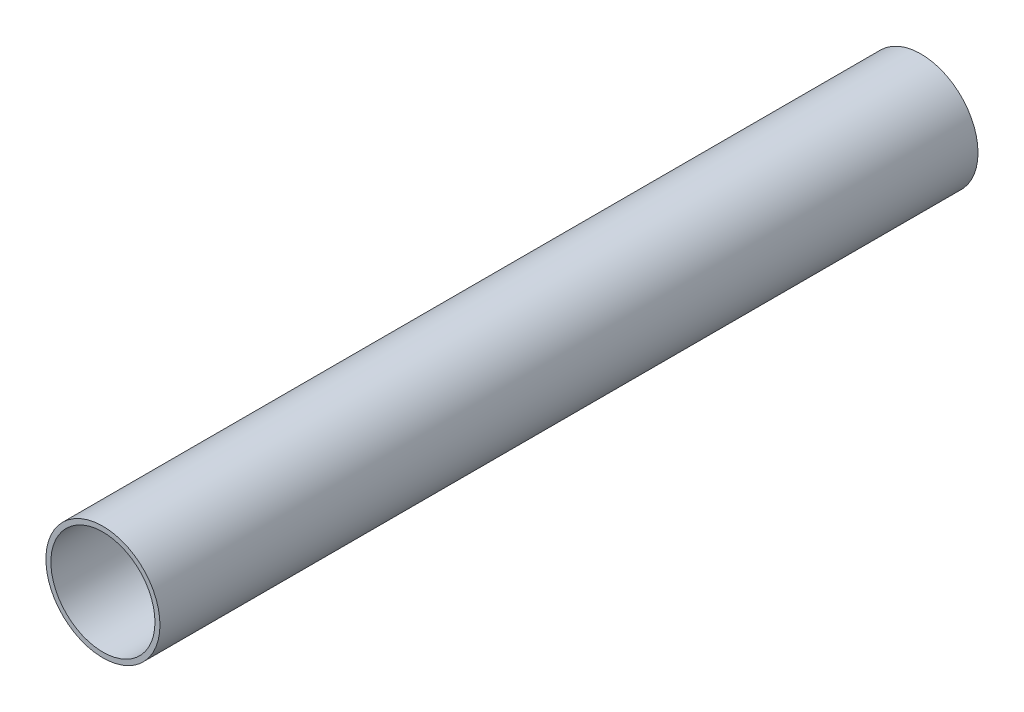
SolidWorks part; units mm, degrees
ref_plane "Front Plane" through (0, 0, 0) normal (0, 0, 1) x (1, 0, 0)
ref_plane "Top Plane" through (0, 0, 0) normal (0, 1, 0) x (1, 0, 0)
ref_plane "Right Plane" through (0, 0, 0) normal (1, 0, 0) x (0, 0, -1)
sketch "Sketch1" plane through (0, 0, 0) normal (0, 0, 1) x (1, 0, 0)
  circle A0 centre (0, 0) radius 15.9385
  circle A1 centre (0, 0) radius 14.5415
  dimension "D1" = 29.083
  dimension "D2" = 31.877
extrude "Boss-Extrude1" add sketch "Sketch1" along normal blind 228.6
